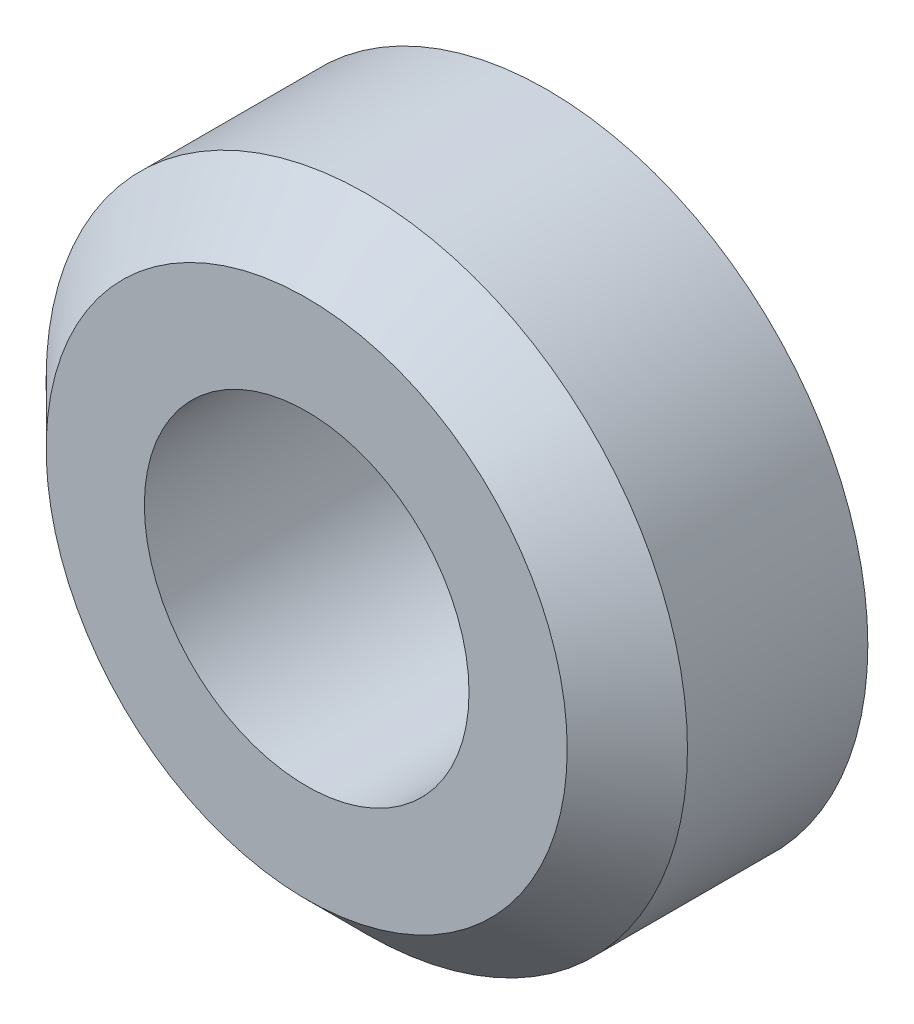
SolidWorks part; units mm, degrees
material "PEI"
ref_plane "Piano frontale" through (0, 0, 0) normal (0, 0, 1) x (1, 0, 0)
ref_plane "Piano superiore" through (0, 0, 0) normal (0, 1, 0) x (1, 0, 0)
ref_plane "Piano destro" through (0, 0, 0) normal (1, 0, 0) x (0, 0, -1)
sketch "Schizzo1" plane through (0, 0, 0) normal (0, 0, 1) x (1, 0, 0)
  circle A0 centre (0, 0) radius 4.05
  circle A1 centre (0, 0) radius 8
  dimension "D1" = 8.1
  dimension "D2" = 16
extrude "Estrusione-Estrusione1" add sketch "Schizzo1" along normal blind 6
chamfer "Smusso1" distance 1.5 angle 45 1 edges at (8, 0, 6)
